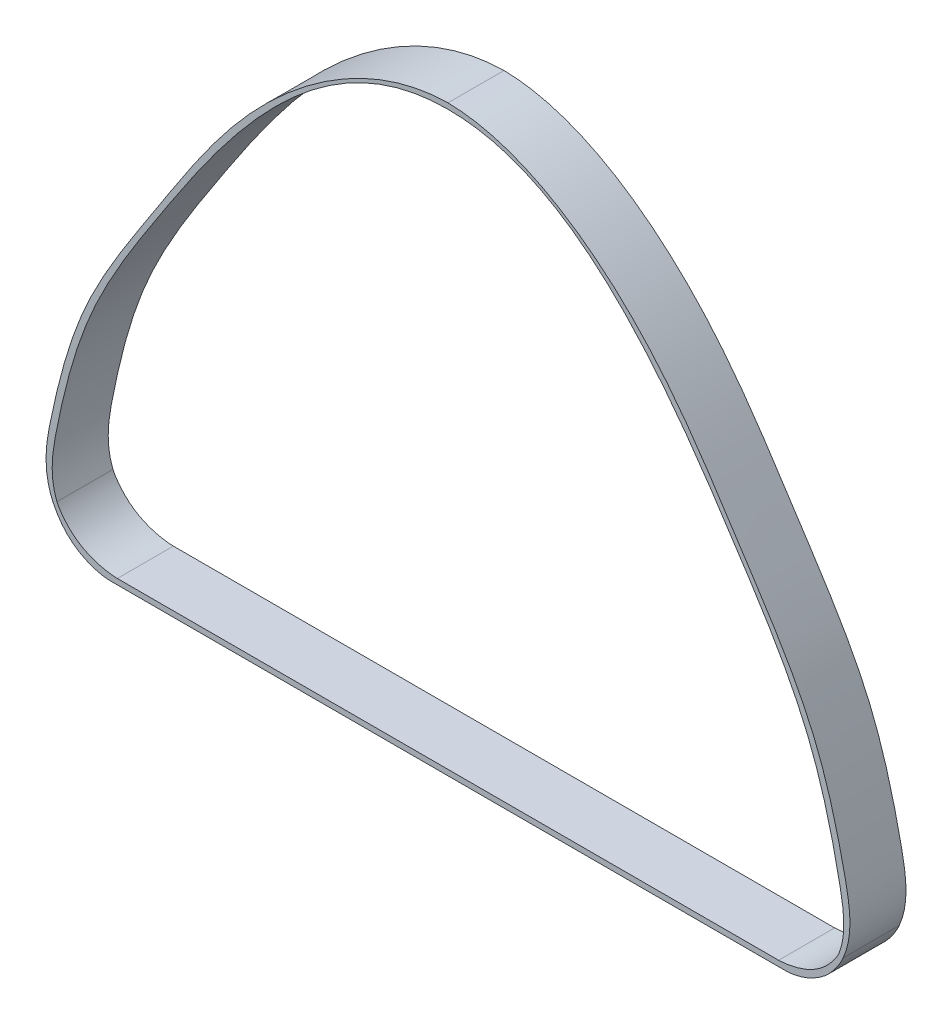
SolidWorks part; units mm, degrees
ref_plane "Front" through (0, 0, 0) normal (0, 0, 1) x (1, 0, 0)
ref_plane "Top" through (0, 0, 0) normal (0, 1, 0) x (1, 0, 0)
ref_plane "Right" through (0, 0, 0) normal (1, 0, 0) x (0, 0, -1)
sketch "草图1" plane through (0, 0, 0) normal (0, 0, 1) x (1, 0, 0)
  line L0 (0, 0) -> (0, -43.6365) construction
  line L1 (0, 0) -> (-54.6361, -25.4772) construction
  line L2 (0, 0) -> (57.9065, -27.0022) construction
  line L3 (-30, -20) -> (30, -20)
  line L4 (-29.5, -19.5) -> (29.5, -19.5)
  spline S0 degree 3 poles (-35.2584, -16.4413) (-34.9964, -17.0209) (-33.6906, -19.1426) (-31.1854, -20.0293) (-30, -20) knots 0 0 0 0 0.359901 1 1 1 1
  spline S1 degree 3 poles (-34.8901, -16.2695) (-34.6657, -16.7781) (-33.0755, -18.9213) (-30.5488, -19.4794) (-29.5, -19.5) knots 0 0 0 0 0.376949 1 1 1 1
  spline S2 degree 3 poles (35.2584, -16.4413) (34.9964, -17.0209) (33.6906, -19.1426) (31.1854, -20.0293) (30, -20) knots 0 0 0 0 0.359901 1 1 1 1
  spline S3 degree 3 poles (34.8901, -16.2695) (34.6657, -16.7781) (33.0755, -18.9213) (30.5488, -19.4794) (29.5, -19.5) knots 0 0 0 0 0.376949 1 1 1 1
  spline S4 degree 3 poles (0, 32) (-6.5255, 31.9036) (-17.5035, 24.3307) (-25.7176, 11.1374) (-32.7912, 0.6069) (-35.2636, -8.8645) (-36.2301, -14.212) (-35.2584, -16.4413) knots 0 0 0 0 0.310762 0.543528 0.745407 0.898184 1 1 1 1
  spline S5 degree 3 poles (0, 31.5) (-7.2551, 31.5111) (-16.9533, 23.7159) (-25.4402, 10.942) (-32.2811, 0.3384) (-34.6769, -8.9912) (-35.6048, -14.4291) (-34.8901, -16.2695) knots 0 0 0 0 0.317686 0.539497 0.743916 0.910984 1 1 1 1
  spline S6 degree 3 poles (0, 31.5) (7.2551, 31.5111) (16.9533, 23.7159) (25.4402, 10.942) (32.2811, 0.3384) (34.6769, -8.9912) (35.6048, -14.4291) (34.8901, -16.2695) knots 0 0 0 0 0.317686 0.539497 0.743916 0.910984 1 1 1 1
  spline S7 degree 3 poles (0, 32) (6.5255, 31.9036) (17.5035, 24.3307) (25.7176, 11.1374) (32.7912, 0.6069) (35.2636, -8.8645) (36.2301, -14.212) (35.2584, -16.4413) knots 0 0 0 0 0.310762 0.543528 0.745407 0.898184 1 1 1 1
  point P17 (0, 31.5)
  point P18 (0, 32)
  point P37 (-17.4481, 21.8213)
  point P38 (-25.6527, 10.5624)
  point P39 (-32, -0.5977)
  point P40 (-34.9109, -10.6788)
  point P41 (-34.8901, -16.2695)
  point P42 (-33.3338, -18.1686)
  dimension "D3" = 65
  dimension "D4" = 32
  dimension "D5" = 20
  dimension "D6" = 60
  dimension "D7" = 31.5
  dimension "D8" = 0.5
  dimension "D9" = 59
extrude "凸台-拉伸1" add sketch "草图1" along normal blind 5
